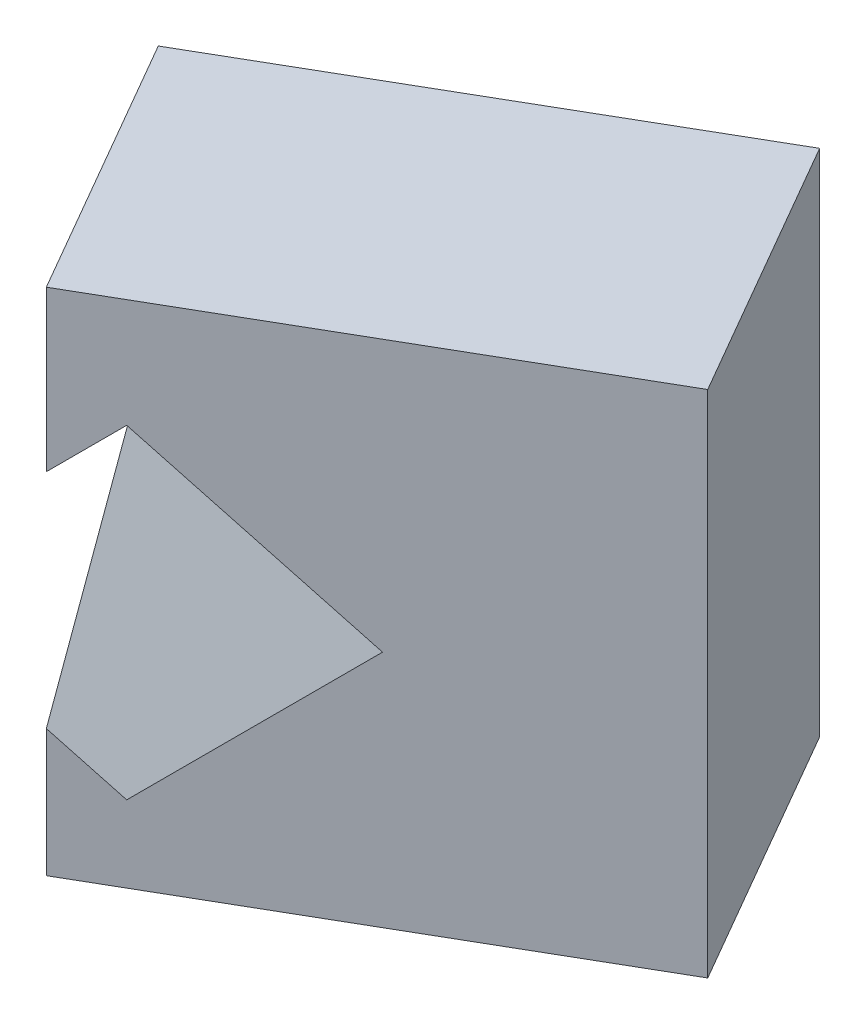
SolidWorks part; units mm, degrees
ref_plane "Front" through (0, 0, 0) normal (0, 0, 1) x (1, 0, 0)
ref_plane "Top" through (0, 0, 0) normal (0, 1, 0) x (1, 0, 0)
ref_plane "Right" through (0, 0, 0) normal (1, 0, 0) x (0, 0, -1)
sketch "Sketch1" plane through (0, 0, 0) normal (0, 1, 0) x (1, 0, 0)
  line L0 (0, 0) -> (30, -51.9615)
  line L1 (30, -51.9615) -> (-52.2724, -99.4615)
  line L2 (-52.2724, -99.4615) -> (-82.2724, -47.5)
  line L3 (-82.2724, -47.5) -> (0, 0)
  line L4 (0, 0) -> (-36.7811, 0) construction
  dimension "D1" = 30
  dimension "D2" = 60
  dimension "D3" = 95
extrude "Extrude1" add sketch "Sketch1" along normal blind 100
sketch "Sketch2" plane through (0, 0, 0) normal (0, 0, 1) x (1, 0, 0)
  line L0 (-42.2724, 78.6396) -> (-10.4526, 46.8198)
  line L1 (-10.4526, 46.8198) -> (-42.2724, 15)
  line L2 (-42.2724, 15) -> (-74.0922, 46.8198)
  line L3 (-74.0922, 46.8198) -> (-42.2724, 78.6396)
  line L4 (-42.2724, 15) -> (-9.3658, 15) construction
  line L5 (-52.2724, 100) -> (-52.2724, 0) construction
  line L6 (-52.2724, 0) -> (30, 0) construction
  dimension "D1" = 45
  dimension "D2" = 45
  dimension "D3" = 10
  dimension "D4" = 15
extrude "Cut-Extrude1" cut sketch "Sketch2" along normal through all
